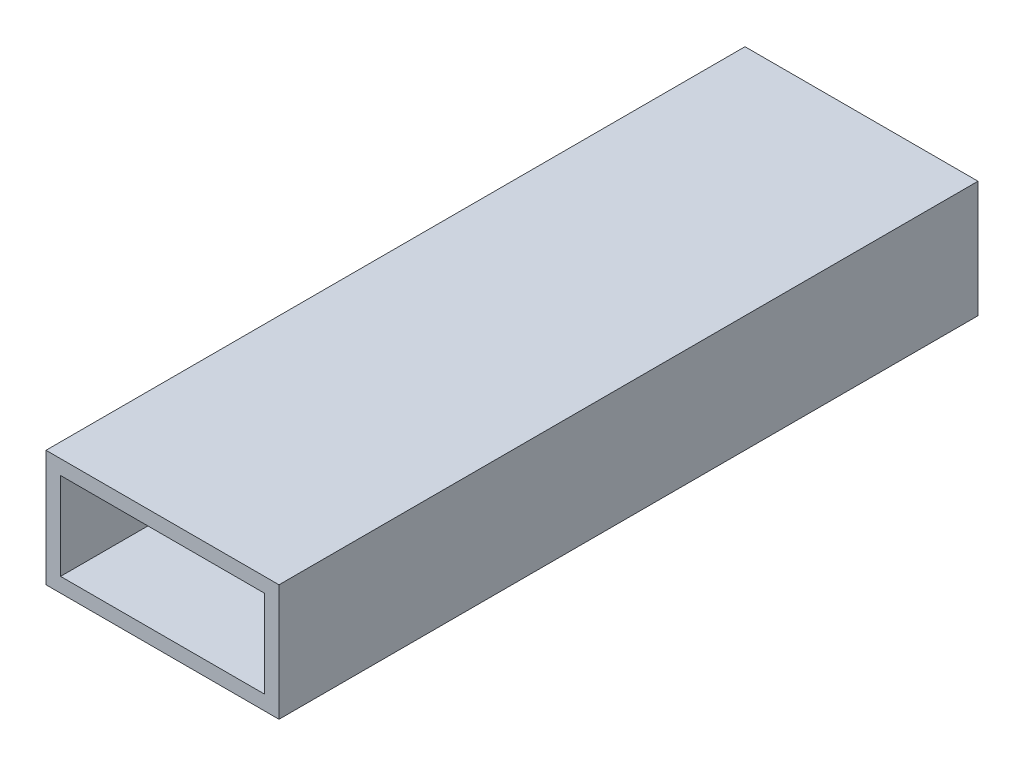
SolidWorks part; units mm, degrees
ref_plane "Front Plane" through (0, 0, 0) normal (0, 0, 1) x (1, 0, 0)
ref_plane "Top Plane" through (0, 0, 0) normal (0, 1, 0) x (1, 0, 0)
ref_plane "Right Plane" through (0, 0, 0) normal (1, 0, 0) x (0, 0, -1)
sketch "Sketch1" plane through (0, 0, 0) normal (0, 0, 1) x (1, 0, 0)
  line L0 (-22.225, -9.525) -> (22.225, -9.525)
  line L1 (-25.4, -12.7) -> (25.4, -12.7)
  line L2 (-25.4, -12.7) -> (-25.4, 12.7)
  line L3 (-25.4, 12.7) -> (25.4, 12.7)
  line L4 (25.4, -12.7) -> (25.4, 12.7)
  line L5 (22.225, -9.525) -> (22.225, 9.525)
  line L6 (-22.225, 9.525) -> (22.225, 9.525)
  line L7 (-22.225, -9.525) -> (-22.225, 9.525)
  dimension "D1" = 25.4
  dimension "D2" = 50.8
  dimension "D3" = 3.175
extrude "Boss-Extrude1" add sketch "Sketch1" along normal blind 152.4
